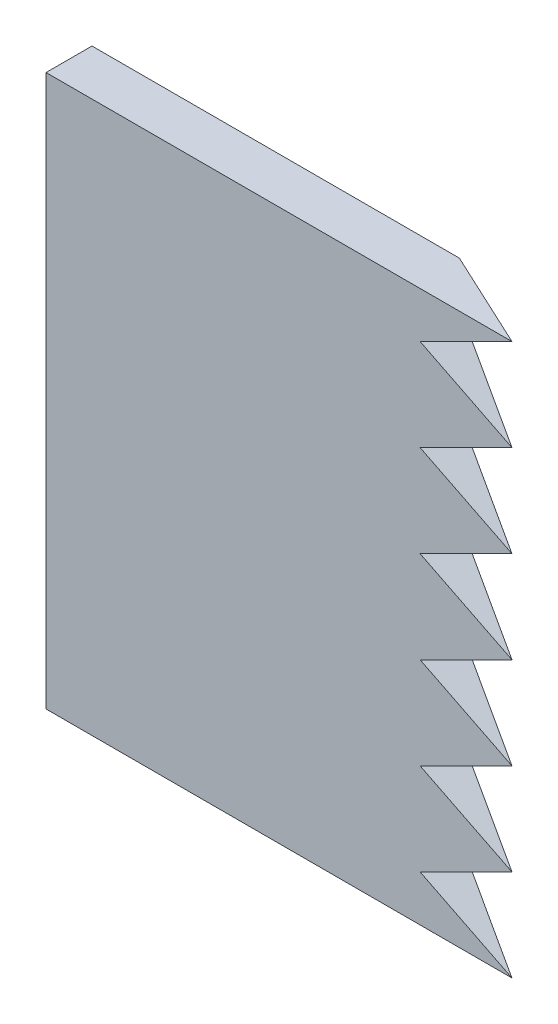
SolidWorks part; units mm, degrees
ref_plane "Front Plane" through (0, 0, 0) normal (0, 0, 1) x (1, 0, 0)
ref_plane "Top Plane" through (0, 0, 0) normal (0, 1, 0) x (1, 0, 0)
ref_plane "Right Plane" through (0, 0, 0) normal (1, 0, 0) x (0, 0, -1)
sketch "Sketch1" plane through (0, 0, 0) normal (0, 1, 0) x (1, 0, 0)
  line L0 (0, 0) -> (0, -146.05) construction
  line L1 (0, 0) -> (64.407, -138.1213) construction
  line L2 (0, -146.05) -> (64.407, -146.05)
  line L3 (0, -146.05) -> (0, -139.7)
  line L4 (64.407, -138.1213) -> (64.407, -146.05) construction
  line L5 (64.407, -146.05) -> (50.7894, -139.7)
  line L6 (0, -139.7) -> (50.7894, -139.7)
  circle A0 centre (0, 0) radius 152.4 construction
  point P5 (0, 0)
  dimension "D1" = 304.8
  dimension "D2" = 25
  dimension "D3" = 25
  dimension "D4" = 146.05
  dimension "D5" = 6.35
extrude "Boss-Extrude1" add sketch "Sketch1" along normal blind 76.2
sketch "Sketch2" plane through (0, 0, 146.05) normal (0, 0, 1) x (1, 0, 0)
  line L0 (64.407, 0) -> (64.407, 76.2) construction
  line L1 (64.407, 76.2) -> (51.707, 69.85)
  line L2 (51.707, 69.85) -> (64.407, 63.5)
  line L3 (64.407, 63.5) -> (64.407, 76.2)
  line L4 (51.707, 69.85) -> (64.407, 69.85) construction
  line L5 (51.707, 57.15) -> (64.407, 50.8)
  line L6 (64.407, 63.5) -> (51.707, 57.15)
  line L7 (64.407, 50.8) -> (64.407, 63.5)
  line L8 (51.707, 44.45) -> (64.407, 38.1)
  line L9 (64.407, 50.8) -> (51.707, 44.45)
  line L10 (64.407, 38.1) -> (64.407, 50.8)
  line L11 (51.707, 31.75) -> (64.407, 25.4)
  line L12 (64.407, 38.1) -> (51.707, 31.75)
  line L13 (64.407, 25.4) -> (64.407, 38.1)
  line L14 (51.707, 19.05) -> (64.407, 12.7)
  line L15 (64.407, 25.4) -> (51.707, 19.05)
  line L16 (64.407, 12.7) -> (64.407, 25.4)
  line L17 (51.707, 6.35) -> (64.407, 0)
  line L18 (64.407, 12.7) -> (51.707, 6.35)
  line L19 (64.407, 0) -> (64.407, 12.7)
  line M8 (64.407, 0) -> (64.407, 76.2)
  dimension "D1" = 12.7
  dimension "D2" = 12.7
  dimension "D3" = 6.35
  dimension "D5" = 19.05
  dimension "D4" = 6
extrude "Cut-Extrude1" cut sketch "Sketch2" against normal through all contours L18 L17 M8 | L15 L14 M8 | L12 L11 M8 | L9 L8 M8 | L6 L5 M8 | L1 L2 M8
